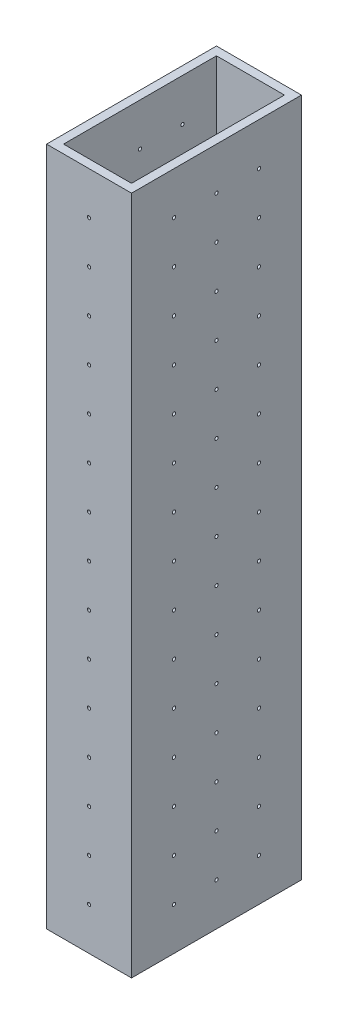
SolidWorks part; units mm, degrees
ref_plane "Front Plane" through (0, 0, 0) normal (0, 0, 1) x (1, 0, 0)
ref_plane "Top Plane" through (0, 0, 0) normal (0, 1, 0) x (1, 0, 0)
ref_plane "Right Plane" through (0, 0, 0) normal (1, 0, 0) x (0, 0, -1)
sketch "Sketch1" plane through (0, 0, 0) normal (0, 1, 0) x (1, 0, 0)
  line L1 (-2.9411, 6.7176) -> (17.3789, 6.7176)
  line L2 (-2.9411, 6.7176) -> (-2.9411, -39.0024)
  line L3 (-2.9411, -39.0024) -> (17.3789, -39.0024)
  line L4 (17.3789, 6.7176) -> (17.3789, -39.0024)
  line L5 (-5.4811, 9.2576) -> (19.9189, 9.2576)
  line L6 (-5.4811, 9.2576) -> (-5.4811, -41.5424)
  line L7 (-5.4811, -41.5424) -> (19.9189, -41.5424)
  line L8 (19.9189, 9.2576) -> (19.9189, -41.5424)
  dimension "D1" = 50.8
  dimension "D2" = 25.4
  dimension "D3" = 2.54
  dimension "D4" = 2.54
  dimension "D5" = 2.54
  dimension "D6" = 2.54
extrude "Boss-Extrude1" add sketch "Sketch1" along normal blind 203.2
sketch "Sketch2" plane through (0, 0, -9.2576) normal (0, 0, -1) x (-1, 0, 0)
  line L1 (-19.9189, 203.2) -> (-19.9189, 0) construction
  line L2 (-19.9189, 203.2) -> (5.4811, 203.2) construction
  circle A0 centre (-7.2189, 190.5) radius 0.5
  circle A1 centre (-7.2189, 177.8) radius 0.5
  circle A2 centre (-7.2189, 165.1) radius 0.5
  circle A3 centre (-7.2189, 152.4) radius 0.5
  circle A4 centre (-7.2189, 139.7) radius 0.5
  circle A5 centre (-7.2189, 127) radius 0.5
  circle A6 centre (-7.2189, 114.3) radius 0.5
  circle A7 centre (-7.2189, 101.6) radius 0.5
  circle A8 centre (-7.2189, 88.9) radius 0.5
  circle A9 centre (-7.2189, 76.2) radius 0.5
  circle A10 centre (-7.2189, 63.5) radius 0.5
  circle A11 centre (-7.2189, 50.8) radius 0.5
  circle A12 centre (-7.2189, 38.1) radius 0.5
  circle A13 centre (-7.2189, 25.4) radius 0.5
  circle A14 centre (-7.2189, 12.7) radius 0.5
  dimension "D1" = 1
  dimension "D2" = 12.7
  dimension "D3" = 12.7
  dimension "D4" = 15
extrude "Cut-Extrude1" cut sketch "Sketch2" against normal up to surface (50.8 mm away) up to face at (7.2189, 101.6, 41.5424)
sketch "Sketch3" plane through (19.9189, 0, 0) normal (1, 0, 0) x (0, 0, -1)
  line L0 (9.2576, 203.2) -> (9.2576, 0) construction
  line L2 (-41.5424, 203.2) -> (9.2576, 203.2) construction
  circle A0 centre (-3.4424, 190.5) radius 0.5
  circle A1 centre (-16.1424, 190.5) radius 0.5
  circle A2 centre (-28.8424, 190.5) radius 0.5
  circle A3 centre (-16.1424, 177.8) radius 0.5
  circle A4 centre (-28.8424, 177.8) radius 0.5
  circle A5 centre (-16.1424, 165.1) radius 0.5
  circle A6 centre (-28.8424, 165.1) radius 0.5
  circle A7 centre (-16.1424, 152.4) radius 0.5
  circle A8 centre (-28.8424, 152.4) radius 0.5
  circle A9 centre (-16.1424, 139.7) radius 0.5
  circle A10 centre (-28.8424, 139.7) radius 0.5
  circle A11 centre (-16.1424, 127) radius 0.5
  circle A12 centre (-28.8424, 127) radius 0.5
  circle A13 centre (-16.1424, 114.3) radius 0.5
  circle A14 centre (-28.8424, 114.3) radius 0.5
  circle A15 centre (-16.1424, 101.6) radius 0.5
  circle A16 centre (-28.8424, 101.6) radius 0.5
  circle A17 centre (-16.1424, 88.9) radius 0.5
  circle A18 centre (-28.8424, 88.9) radius 0.5
  circle A19 centre (-16.1424, 76.2) radius 0.5
  circle A20 centre (-28.8424, 76.2) radius 0.5
  circle A21 centre (-16.1424, 63.5) radius 0.5
  circle A22 centre (-28.8424, 63.5) radius 0.5
  circle A23 centre (-16.1424, 50.8) radius 0.5
  circle A24 centre (-28.8424, 50.8) radius 0.5
  circle A25 centre (-16.1424, 38.1) radius 0.5
  circle A26 centre (-28.8424, 38.1) radius 0.5
  circle A27 centre (-3.4424, 177.8) radius 0.5
  circle A28 centre (-3.4424, 165.1) radius 0.5
  circle A29 centre (-3.4424, 152.4) radius 0.5
  circle A30 centre (-3.4424, 139.7) radius 0.5
  circle A31 centre (-3.4424, 127) radius 0.5
  circle A32 centre (-3.4424, 114.3) radius 0.5
  circle A33 centre (-3.4424, 101.6) radius 0.5
  circle A34 centre (-3.4424, 88.9) radius 0.5
  circle A35 centre (-3.4424, 76.2) radius 0.5
  circle A36 centre (-3.4424, 63.5) radius 0.5
  circle A37 centre (-3.4424, 50.8) radius 0.5
  circle A38 centre (-3.4424, 38.1) radius 0.5
  circle A39 centre (-3.4424, 25.4) radius 0.5
  circle A40 centre (-16.1424, 25.4) radius 0.5
  circle A41 centre (-28.8424, 25.4) radius 0.5
  circle A42 centre (-3.4424, 12.7) radius 0.5
  circle A43 centre (-16.1424, 12.7) radius 0.5
  circle A44 centre (-28.8424, 12.7) radius 0.5
  dimension "D1" = 1
  dimension "D2" = 12.7
  dimension "D3" = 12.7
  dimension "D4" = 3
  dimension "D5" = 15
extrude "Cut-Extrude2" cut sketch "Sketch3" against normal up to surface (25.4 mm away) up to face at (-5.4811, 101.6, 16.1424)
